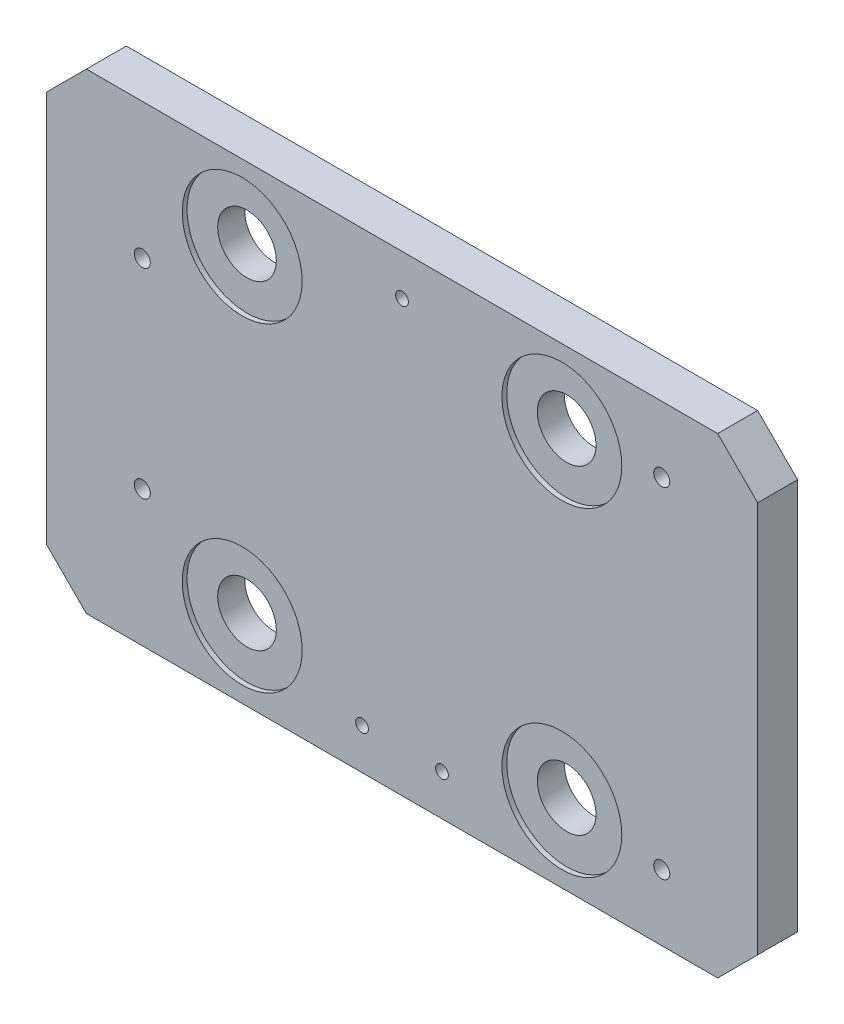
SolidWorks part; units mm, degrees
material "AISI 304"
ref_plane "Front" through (0, 0, 0) normal (0, 0, 1) x (1, 0, 0)
ref_plane "Top" through (0, 0, 0) normal (0, 1, 0) x (1, 0, 0)
ref_plane "Right" through (0, 0, 0) normal (1, 0, 0) x (0, 0, -1)
ref_plane "Plane1" through (0, 0, 16.51) normal (0, 0, 1) x (1, 0, 0)
sketch "Sketch3" plane through (0, 0, 0) normal (0, 0, 1) x (1, 0, 0)
  line L1 (0, 0) -> (226.06, 0)
  line L2 (0, 0) -> (0, -149.86)
  line L3 (0, -149.86) -> (226.06, -149.86)
  line L4 (226.06, 0) -> (226.06, -149.86)
  dimension "D1" = 226.06
  dimension "D2" = 149.86
extrude "Extrude2" add sketch "Sketch3" along normal blind 12.7
sketch "Sketch20" plane through (0, 0, 12.7) normal (0, 0, 1) x (1, 0, 0)
  line L0 (163.83, -125.73) -> (62.23, -125.73) construction
  line L1 (163.83, -125.73) -> (163.83, -24.13) construction
  line L2 (163.83, -24.13) -> (62.23, -24.13) construction
  line L3 (62.23, -125.73) -> (62.23, -24.13) construction
  line L4 (113.03, -149.86) -> (113.03, -125.73) construction
  line L5 (0, -149.86) -> (226.06, -149.86) construction
  line L6 (0, -74.93) -> (62.23, -74.93) construction
  line L7 (0, 0) -> (0, -149.86) construction
  circle A0 centre (163.83, -125.73) radius 19.05
  circle A3 centre (62.23, -125.73) radius 19.05
  circle A5 centre (163.83, -24.13) radius 19.05
  circle A7 centre (62.23, -24.13) radius 19.05
  dimension "D1" = 38.1
  dimension "D2" = 101.6
  dimension "D3" = 101.6
hole_wizard "1/4-20 Tapped Hole1" positions "Sketch13" profile "Sketch12" tap size "1/4-20" standard "Ansi Inch" end condition through all
sketch "Sketch13" plane through (0, 0, 0) normal (0, 0, -1) x (-1, 0, 0)
  line L0 (-226.06, -74.93) -> (0, -74.93) construction
  line L1 (-226.06, -149.86) -> (-226.06, 0) construction
  line L2 (0, 0) -> (0, -149.86) construction
  line L4 (-113.03, 0) -> (-113.03, -149.86) construction
  line L5 (-226.06, 0) -> (0, 0) construction
  line L6 (0, -149.86) -> (-226.06, -149.86) construction
  line L11 (-195.58, -20.955) -> (-195.58, -74.93) construction
  line L13 (-195.58, -74.93) -> (-195.58, -128.905) construction
  line L15 (-30.48, -43.18) -> (-30.48, -74.93) construction
  line L17 (-30.48, -74.93) -> (-30.48, -106.68) construction
  point P3 (-195.58, -20.955)
  point P5 (-195.58, -128.905)
  point P7 (-30.48, -43.18)
  point P9 (-30.48, -106.68)
  dimension "D1" = 82.55
  dimension "D2" = 82.55
  dimension "D3" = 107.95
  dimension "D4" = 63.5
sketch "Sketch12" plane through (195.58, -20.955, 0) normal (1, 0, 0) x (0, 1, 0)
  line L0 (0, 0) -> (0, 12.7)
  line L1 (0, 12.7) -> (2.5527, 12.7)
  line L2 (2.5527, 12.7) -> (2.5527, 0)
  line L5 (2.5527, 0) -> (0, 0)
  line L11 (0, -6.35) -> (0, 107.95) construction
  dimension "Thru Tap Drill Dia." = 5.1054
  dimension "Thru Tap Drill Depth" = 12.7
cosmetic thread "Hole Thread5" parameters "D2"=6.35
cosmetic thread "Hole Thread6" parameters "D2"=6.35
cosmetic thread "Hole Thread7" parameters "D2"=6.35
cosmetic thread "Hole Thread8" parameters "D2"=6.35
hole_wizard "CBORE for 5/8 Socket Head Cap Screw1" positions "3DSketch6" profile "Sketch14" counterbore size "5/8" standard "Ansi Inch" end condition through all
sketch3d "3DSketch6"
  line L0 (113.03, 0, 0) -> (113.03, -149.86, 0) construction
  line L1 (226.06, 0, 0) -> (0, 0, 0) construction
  line L2 (0, -149.86, 0) -> (226.06, -149.86, 0) construction
  line L4 (0, -74.93, 0) -> (226.06, -74.93, 0) construction
  line L5 (0, 0, 0) -> (0, -149.86, 0) construction
  line L6 (226.06, -149.86, 0) -> (226.06, 0, 0) construction
  line L7 (163.83, -24.13, 0) -> (163.83, -74.93, 0) construction
  line L9 (163.83, -74.93, 0) -> (163.83, -125.73, 0) construction
  line L17 (163.83, -24.13, 0) -> (113.03, -24.13, 0) construction
  line L20 (113.03, -24.13, 0) -> (62.23, -24.13, 0) construction
  point P0 (163.83, -24.13, 0)
  point P2 (62.23, -24.13, 0)
  point P4 (62.23, -125.73, 0)
  point P6 (163.83, -125.73, 0)
  dimension "D1" = 101.6
  dimension "D2" = 101.6
sketch "Sketch14" plane through (163.83, -24.13, 0) normal (1, 0, 0) x (0, 1, 0)
  line L0 (0, 0) -> (0, 12.7)
  line L1 (0, 12.7) -> (9.3218, 12.7)
  line L3 (9.3218, 12.7) -> (9.3218, 2.54)
  line L4 (9.3218, 2.54) -> (19.05, 2.54)
  line L5 (19.05, 2.54) -> (19.05, 0)
  line L7 (19.05, 0) -> (0, 0)
  line L11 (0, -6.35) -> (0, 107.95) construction
  dimension "Thru Hole Dia." = 18.6436
  dimension "Thru Hole Depth" = 12.7
  dimension "C'Bore Dia." = 38.1
  dimension "C'Bore Depth" = 2.54
sketch "Sketch15" plane through (0, 0, 0) normal (0, 0, -1) x (-1, 0, 0)
  line L0 (0, -149.86) -> (-226.06, -149.86) construction
  line L1 (-226.06, 0) -> (0, 0) construction
  line L10 (-113.03, 0) -> (-113.03, -149.86) construction
  line L16 (-113.03, -13.0048) -> (-113.03, -74.93) construction
  line L17 (-125.73, -136.8552) -> (-100.33, -136.8552) construction
  point P0 (-125.73, -136.8552)
  point P1 (-113.03, -13.0048)
  point P54 (-100.33, -136.8552)
  dimension "D1" = 61.9252
  dimension "D2" = 25.4
  dimension "D3" = 12.7
  dimension "D4" = 61.9252
hole_wizard "#10-32 Tapped Hole1" positions "Sketch17" profile "Sketch18" tap size "#10-32" standard "Ansi Inch" end condition through all
sketch "Sketch17" plane through (0, 0, 0) normal (0, 0, -1) x (-1, 0, 0)
  line L0 (-125.73, -136.8552) -> (-100.33, -136.8552) construction
  point P0 (-113.03, -13.0048)
  point P1 (-125.73, -136.8552)
  point P4 (-100.33, -136.8552)
  dimension "D1" = 25.4
sketch "Sketch18" plane through (113.03, -13.0048, 0) normal (1, 0, 0) x (0, 1, 0)
  line L0 (0, 0) -> (0, 12.7)
  line L1 (0, 12.7) -> (2.0193, 12.7)
  line L2 (2.0193, 12.7) -> (2.0193, 0)
  line L5 (2.0193, 0) -> (0, 0)
  line L11 (0, -6.35) -> (0, 107.95) construction
  dimension "Thru Tap Drill Dia." = 4.0386
  dimension "Thru Tap Drill Depth" = 12.7
cosmetic thread "Hole Thread9" parameters "D2"=4.826
cosmetic thread "Hole Thread10" parameters "D2"=4.826
cosmetic thread "Hole Thread11" parameters "D2"=4.826
chamfer "Chamfer1" distance 12.7 angle 45 4 edges at (0, -149.86, 6.35) (226.06, 0, 6.35) (226.06, -149.86, 6.35) (0, 0, 6.35)
extrude "Cut-Extrude5" cut sketch "Sketch20" against normal blind 1.524
